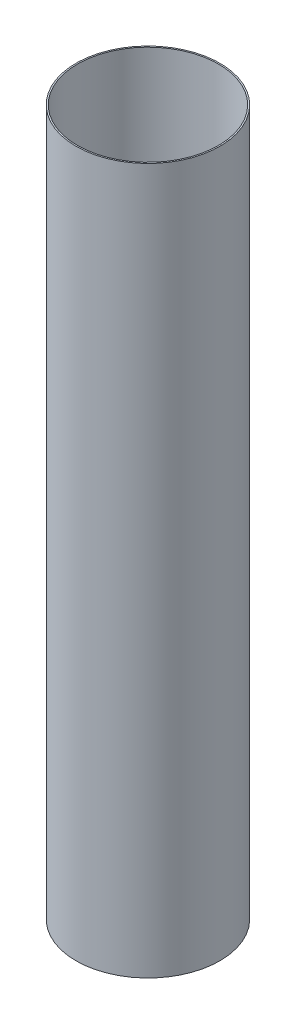
SolidWorks part; units mm, degrees
ref_plane "Alzado" through (0, 0, 0) normal (0, 0, 1) x (1, 0, 0)
ref_plane "Planta" through (0, 0, 0) normal (0, 1, 0) x (1, 0, 0)
ref_plane "Vista lateral" through (0, 0, 0) normal (1, 0, 0) x (0, 0, -1)
sketch "Croquis1" plane through (0, 0, 0) normal (0, 1, 0) x (1, 0, 0)
  circle A0 centre (0, 0) radius 150
  circle A1 centre (0, 0) radius 153
extrude "Saliente-Extruir1" add sketch "Croquis1" along normal blind 1500
